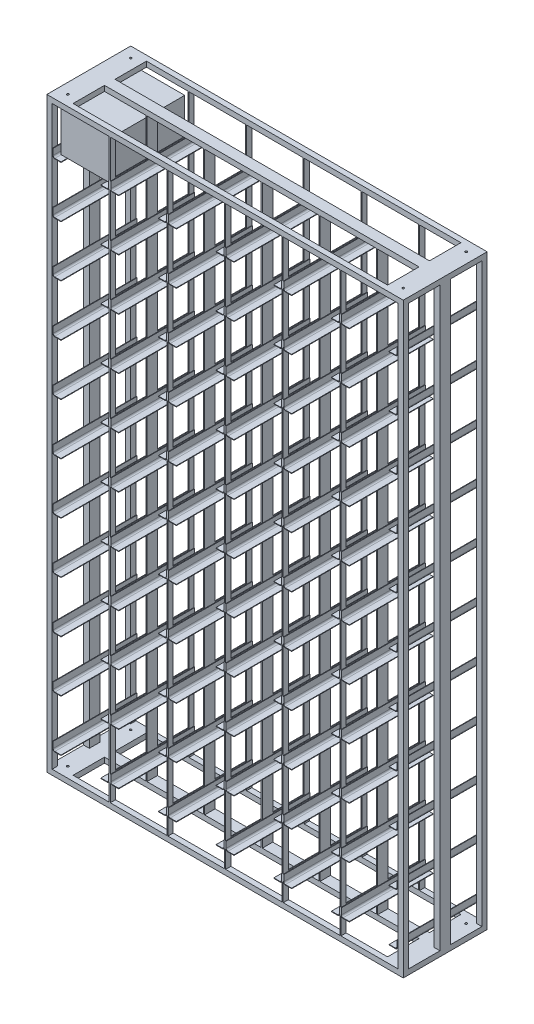
SolidWorks part; units mm, degrees
ref_plane "Front Plane" through (0, 0, 0) normal (0, 0, 1) x (1, 0, 0)
ref_plane "Top Plane" through (0, 0, 0) normal (0, 1, 0) x (1, 0, 0)
ref_plane "Right Plane" through (0, 0, 0) normal (1, 0, 0) x (0, 0, -1)
sketch "Sketch1" plane through (0, 0, 0) normal (0, 1, 0) x (1, 0, 0)
  line L0 (0, 602.3006) -> (0, -719.6319) construction
  line L1 (-1097.6994, 0) -> (1238.4969, 0) construction
  line L2 (-850, 200) -> (-825, 200)
  line L3 (-850, 200) -> (-850, -200)
  line L4 (-850, -200) -> (-825, -200)
  line L5 (-825, 200) -> (-825, -200)
  line L6 (825, 25) -> (825, -25)
  line L7 (-825, 25) -> (825, 25)
  line L8 (-825, 25) -> (-825, -25)
  line L9 (-825, -25) -> (825, -25)
  line L10 (825, 200) -> (825, -200)
  line L11 (850, -200) -> (825, -200)
  line L12 (850, 200) -> (850, -200)
  line L13 (850, 200) -> (825, 200)
  point P14 (0, -25)
  point P15 (0, 25)
  dimension "D1" = 850
  dimension "D2" = 400
  dimension "D3" = 25
  dimension "D4" = 50
extrude "Boss-Extrude1" add sketch "Sketch1" along normal blind 25 contours L5 L2 L3 L4 | L12 L13 L10 L6 L11
sketch "Sketch2" plane through (0, 25, 0) normal (0, 1, 0) x (1, 0, 0)
  line L0 (-850, 200) -> (-850, -200) construction
  line L1 (-822.5, 25) -> (-850, 25)
  line L2 (-822.5, 25) -> (-822.5, -2.5)
  line L3 (-822.5, -2.5) -> (-822.5, -25)
  line L4 (-850, 25) -> (-850, 0)
  line L5 (-725.5626, 0) -> (-912.9084, 0) construction
  line L6 (-822.5, -25) -> (-850, -25)
  line L7 (-850, -25) -> (-850, 0)
  dimension "D1" = 27.5
extrude "Boss-Extrude2" add sketch "Sketch2" along normal blind 1375
mirror "Mirror1" about plane through (0, 0, 0) normal (1, 0, 0) of "Boss-Extrude2"
ref_plane "Plane1" through (0, 1400, 0) normal (0, 1, 0) x (1, 0, 0)
mirror "Mirror5" about plane through (0, 1400, 0) normal (0, 1, 0) of "Mirror1", "Boss-Extrude2"
mirror "Mirror6" about plane through (0, 1400, 0) normal (0, 1, 0) of "Boss-Extrude1", "Mirror5"
sketch "Sketch3" plane through (-825, 0, 0) normal (1, 0, 0) x (0, 0, -1)
  line L1 (-200, 25) -> (-25, 25)
  line L2 (-200, 25) -> (-200, 0)
  line L3 (-200, 0) -> (-25, 0)
  line L4 (-25, 25) -> (-25, 0)
  line L5 (25, 25) -> (200, 25)
  line L6 (25, 25) -> (25, 0)
  line L7 (25, 0) -> (200, 0)
  line L8 (200, 25) -> (200, 0)
extrude "Boss-Extrude3" add sketch "Sketch3" along normal blind 75
mirror "Mirror7" about plane through (0, 0, 0) normal (1, 0, 0) of "Boss-Extrude3"
mirror "Mirror8" about plane through (0, 1400, 0) normal (0, 1, 0) of "Boss-Extrude3", "Mirror7"
sketch "Sketch4" plane through (0, 25, 0) normal (0, 1, 0) x (1, 0, 0)
  line L0 (-850, -200) -> (-750, -200) construction
  line L1 (0, 0) -> (-105.6588, 0) construction
  line L2 (0, 0) -> (0, 80.5015) construction
  circle A0 centre (-800, -150) radius 5
  circle A1 centre (-800, 150) radius 5
  circle A2 centre (800, 150) radius 5
  circle A3 centre (800, -150) radius 5
  dimension "D1" = 10
  dimension "D2" = 50
extrude "Cut-Extrude1" cut sketch "Sketch4" against normal through all
mirror "Mirror9" about plane through (0, 1400, 0) normal (0, 1, 0) of "Cut-Extrude1"
sketch "Sketch5" plane through (0, 25, 0) normal (0, 1, 0) x (1, 0, 0)
  line L0 (-66.5515, 0) -> (113.475, 0) construction
  line L1 (-850, -200) -> (-825, -200)
  line L2 (-850, -200) -> (-850, -175)
  line L3 (-850, -175) -> (-825, -175)
  line L4 (-825, -200) -> (-825, -175)
  line L5 (0, 86.1632) -> (0, -133.5933) construction
  line L6 (-850, 200) -> (-825, 200)
  line L7 (-850, 200) -> (-850, 175)
  line L8 (-850, 175) -> (-825, 175)
  line L9 (-825, 200) -> (-825, 175)
  line L10 (850, -200) -> (850, -175)
  line L11 (850, -200) -> (825, -200)
  line L12 (825, -200) -> (825, -175)
  line L13 (850, -175) -> (825, -175)
  line L14 (850, 200) -> (850, 175)
  line L15 (850, 200) -> (825, 200)
  line L16 (825, 200) -> (825, 175)
  line L17 (850, 175) -> (825, 175)
  dimension "D1" = 25
  dimension "D2" = 25
extrude "Boss-Extrude4" add sketch "Sketch5" along normal up to next
sketch "Sketch6" plane through (-750, 0, 0) normal (1, 0, 0) x (0, 0, -1)
  line L0 (0, 2871.5985) -> (0, 2057.1139) construction
  line L1 (-200, 2800) -> (-175, 2800)
  line L2 (-200, 2800) -> (-200, 2775)
  line L3 (-200, 2775) -> (-175, 2775)
  line L4 (-175, 2800) -> (-175, 2775)
  line L5 (-410.2203, 1400) -> (672.4256, 1400) construction
  line L6 (175, 2800) -> (175, 2775)
  line L7 (200, 2775) -> (175, 2775)
  line L8 (200, 2800) -> (200, 2775)
  line L9 (200, 2800) -> (175, 2800)
  line L10 (200, 0) -> (175, 0)
  line L11 (200, 0) -> (200, 25)
  line L12 (200, 25) -> (175, 25)
  line L13 (175, 0) -> (175, 25)
  line L14 (-175, 0) -> (-175, 25)
  line L15 (-200, 25) -> (-175, 25)
  line L16 (-200, 0) -> (-200, 25)
  line L17 (-200, 0) -> (-175, 0)
extrude "Boss-Extrude5" add sketch "Sketch6" along normal up to next
ref_plane "Plane2" through (-552.5, 0, 0) normal (1, 0, 0) x (0, 0, -1)
sketch "Sketch7" plane through (-552.5, 0, 0) normal (1, 0, 0) x (0, 0, -1)
  line L1 (-25, 2775) -> (25, 2775)
  line L2 (-25, 2775) -> (-25, 25)
  line L3 (-25, 25) -> (25, 25)
  line L4 (25, 2775) -> (25, 25)
extrude "Boss-Extrude6" add sketch "Sketch7" along normal blind 5
pattern_linear "LPattern1" count 5 spacing 275 along (1, 0, 0) of "Boss-Extrude6"
sketch "Sketch9" plane through (0, 0, 0) normal (0, 0, 1) x (1, 0, 0)
  line L2 (-822.5, 2592.5) -> (-820, 2592.5)
  line L3 (-822.5, 2592.5) -> (-822.5, 2563)
  line L4 (-812, 2552.5) -> (-782.5, 2552.5)
  line L5 (-820, 2592.5) -> (-820, 2563)
  line L6 (-825, 2775) -> (825, 2775) construction
  line L7 (-812, 2555) -> (-782.5, 2555)
  line L8 (-592.5, 2552.5) -> (-563, 2552.5)
  line L10 (-782.5, 2555) -> (-782.5, 2552.5)
  line L12 (-687.5, 2786.6243) -> (-687.5, 2678.9769) construction
  line L13 (-592.5, 2555) -> (-592.5, 2552.5)
  line L16 (-563.5, 2555) -> (-592.5, 2555)
  line L17 (-555, 2592.5) -> (-555, 2563.5)
  line L19 (-552.5, 2592.5) -> (-552.5, 2563)
  line L20 (-552.5, 2592.5) -> (-555, 2592.5)
  arc A0 (-812, 2555) -> (-820, 2563) centre (-812, 2563) cw
  arc A1 (-812, 2552.5) -> (-822.5, 2563) centre (-812, 2563) cw
  arc A2 (-552.5, 2563) -> (-563, 2552.5) centre (-563, 2563) cw
  arc A3 (-563.5, 2555) -> (-555, 2563.5) centre (-563.5, 2563.5) ccw
  point P5 (-820, 2555)
  point P13 (-822.5, 2552.5)
  point P25 (-555, 2555)
  dimension "D6" = 8
  dimension "D7" = 10.5
  dimension "D8" = 10.5
  dimension "D9" = 8.5
  dimension "D1" = 40
  dimension "D2" = 40
  dimension "D3" = 2.5
  dimension "D4" = 2.5
  dimension "D5" = 220
extrude "Boss-Extrude7" add sketch "Sketch9" along normal blind 200 and the other way blind 200
pattern_linear "LPattern2" count 6 spacing 275 along (1, 0, 0) count 11 spacing 245 along (0, -1, 0) of "Boss-Extrude7"
sketch "Sketch12" plane through (0, 25, 0) normal (0, 1, 0) x (1, 0, 0)
  line L0 (750, -175) -> (-750, -175) construction
  line L1 (-552.5, -175) -> (-547.5, -175)
  line L2 (-552.5, -175) -> (-552.5, -200)
  line L3 (-552.5, -200) -> (-547.5, -200)
  line L4 (-547.5, -175) -> (-547.5, -200)
  line L5 (-552.5, -25) -> (-552.5, -200) construction
  line L6 (-302.6023, 0) -> (-109.5107, 0) construction
  line L7 (-547.5, 175) -> (-547.5, 200)
  line L8 (-552.5, 200) -> (-547.5, 200)
  line L9 (-552.5, 175) -> (-552.5, 200)
  line L10 (-552.5, 175) -> (-547.5, 175)
extrude "Boss-Extrude8" add sketch "Sketch12" along normal up to next (2750 mm away)
pattern_linear "LPattern3" count 5 spacing 275 along (1, 0, 0) of "Boss-Extrude8"
sketch "Sketch13" plane through (0, 0, 0) normal (0, 0, 1) x (1, 0, 0)
  line L0 (-782.5, 2555) -> (-812, 2555) construction
  line L1 (-812.5, 2555) -> (-562.5, 2555)
  line L2 (-812.5, 2555) -> (-812.5, 2755)
  line L3 (-812.5, 2755) -> (-562.5, 2755)
  line L4 (-562.5, 2555) -> (-562.5, 2755)
  line L6 (-820, 2563) -> (-820, 2592.5) construction
  dimension "D1" = 200
  dimension "D2" = 250
  dimension "D3" = 7.5
extrude "Boss-Extrude9" add sketch "Sketch13" along normal blind 170 and the other way blind 170
